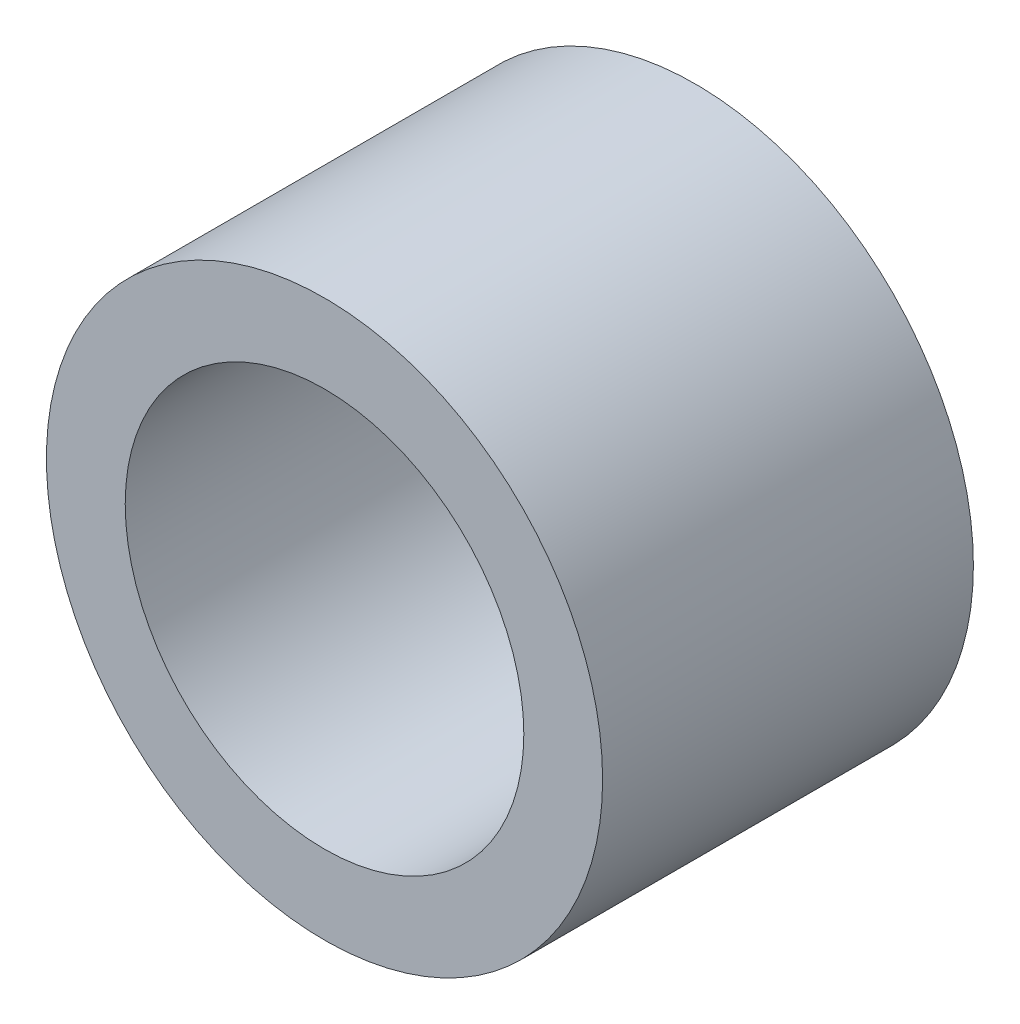
SolidWorks part; units mm, degrees
material "Custom Plastic"
ref_plane "Front Plane" through (0, 0, 0) normal (0, 0, 1) x (1, 0, 0)
ref_plane "Top Plane" through (0, 0, 0) normal (0, 1, 0) x (1, 0, 0)
ref_plane "Right Plane" through (0, 0, 0) normal (1, 0, 0) x (0, 0, -1)
sketch "Sketch1" plane through (0, 0, 0) normal (0, 0, 1) x (1, 0, 0)
  circle A0 centre (0, 0) radius 2.15
  circle A1 centre (0, 0) radius 3
  dimension "D1" = 4.3
  dimension "D2" = 6
extrude "Boss-Extrude1" add sketch "Sketch1" along normal blind 4
